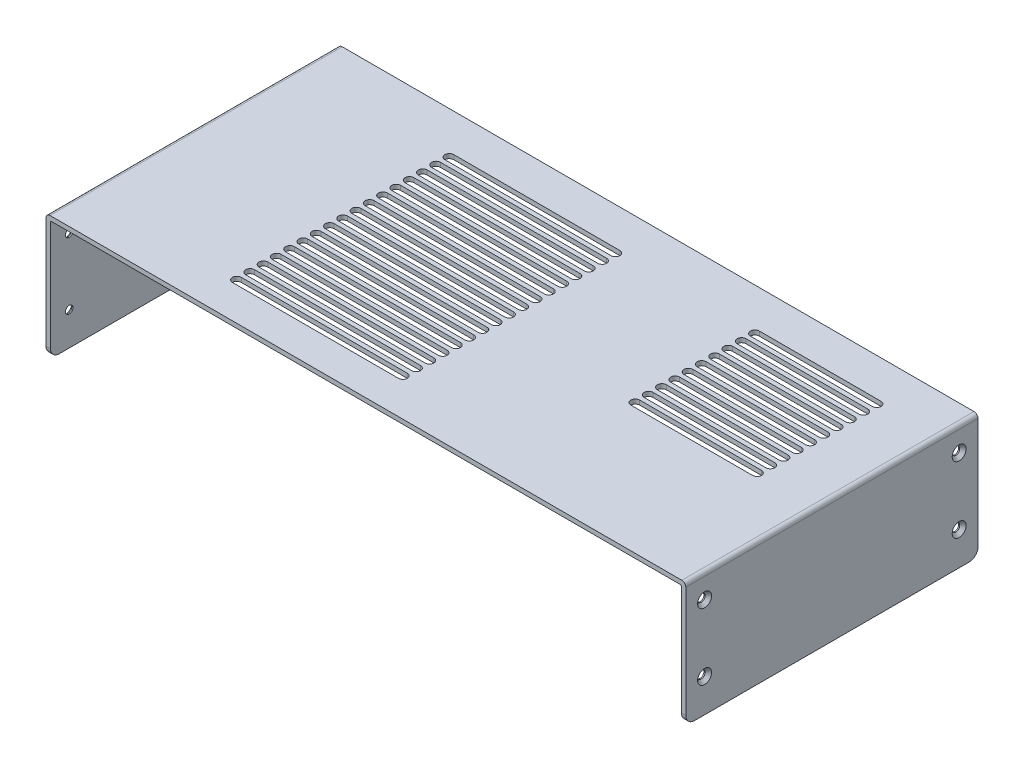
SolidWorks part; units mm, degrees
ref_plane "Front Plane" through (0, 0, 0) normal (0, 0, 1) x (1, 0, 0)
ref_plane "Top Plane" through (0, 0, 0) normal (0, 1, 0) x (1, 0, 0)
ref_plane "Right Plane" through (0, 0, 0) normal (1, 0, 0) x (0, 0, -1)
sketch "Sketch1" plane through (0, 0, 0) normal (0, 0, 1) x (1, 0, 0)
  line L0 (0, 0) -> (-2, 0)
  line L1 (-2, 0) -> (-2, 54.2)
  line L2 (-0.2, 56) -> (285.2, 56)
  line L3 (287, 54.2) -> (287, 0)
  line L4 (287, 0) -> (285, 0)
  line L5 (285, 0) -> (285, 53.5)
  line L6 (284.5, 54) -> (0.5, 54)
  line L7 (0, 53.5) -> (0, 0)
  arc A0 (285, 53.5) -> (284.5, 54) centre (284.5, 53.5) ccw
  arc A1 (0.5, 54) -> (0, 53.5) centre (0.5, 53.5) ccw
  arc A2 (-2, 54.2) -> (-0.2, 56) centre (-0.2, 54.2) cw
  arc A3 (285.2, 56) -> (287, 54.2) centre (285.2, 54.2) cw
  point P13 (0, 54)
  dimension "D5" = 0.5
  dimension "D6" = 1.8
  dimension "D1" = 54
  dimension "D2" = 285
  dimension "D3" = 2
  dimension "D4" = 2
extrude "Boss-Extrude1" add sketch "Sketch1" along normal blind 132
hole_wizard "CSK for M3 Flat Head Machine Screw1" positions "Sketch3" profile "Sketch2" countersink size "M3" standard "Ansi Metric"
sketch "Sketch3" plane through (-2, 0, 0) normal (-1, 0, 0) x (0, 0, 1)
  point P0 (8.5, 45)
  point P1 (8.5, 15)
  point P3 (123.5, 45)
  point P5 (123.5, 15)
sketch "Sketch2" plane through (-2, 45, 8.5) normal (0, 1, 0) x (0, 0, 1)
  line L0 (0, 0) -> (0, 6.0215)
  line L1 (0, 6.0215) -> (1.7, 5)
  line L2 (1.7, 5) -> (1.7, 1.45)
  line L3 (1.7, 1.45) -> (3.15, 0)
  line L5 (3.15, 0) -> (0, 0)
  line L6 (-1.7, 1.45) -> (-3.15, 0) construction
  line L10 (0, 6.0215) -> (-1.7, 5) construction
  line L11 (0, -6.35) -> (0, 107.95) construction
  dimension "Hole Dia." = 3.4
  dimension "Hole Depth" = 5
  dimension "Near C'Sink Dia." = 6.3
  dimension "Near C'Sink Angle" = 90
  dimension "Drill Angle" = 118
hole_wizard "CSK for M3 Flat Head Machine Screw2" positions "Sketch5" profile "Sketch4" countersink size "M3" standard "Ansi Metric"
sketch "Sketch5" plane through (287, 0, 0) normal (1, 0, 0) x (0, 0, -1)
  point P0 (-123.5, 45)
  point P1 (-123.5, 15)
  point P3 (-8.5, 45)
  point P5 (-8.5, 15)
sketch "Sketch4" plane through (287, 45, 123.5) normal (0, 1, 0) x (0, 0, -1)
  line L0 (0, 0) -> (0, 6.0215)
  line L1 (0, 6.0215) -> (1.7, 5)
  line L2 (1.7, 5) -> (1.7, 1.45)
  line L3 (1.7, 1.45) -> (3.15, 0)
  line L5 (3.15, 0) -> (0, 0)
  line L6 (-1.7, 1.45) -> (-3.15, 0) construction
  line L10 (0, 6.0215) -> (-1.7, 5) construction
  line L11 (0, -6.35) -> (0, 107.95) construction
  dimension "Hole Dia." = 3.4
  dimension "Hole Depth" = 5
  dimension "Near C'Sink Dia." = 6.3
  dimension "Near C'Sink Angle" = 90
  dimension "Drill Angle" = 118
sketch "Sketch6" plane through (0, 56, 0) normal (0, 1, 0) x (1, 0, 0)
  line L0 (67.2, -19) -> (142.2, -19) construction
  line L1 (67.2, -17) -> (142.2, -17)
  line L2 (67.2, -21) -> (142.2, -21)
  line L3 (285.2, 0) -> (-0.2, 0) construction
  line L6 (285.2, -132) -> (285.2, 0) construction
  arc A0 (67.2, -17) -> (67.2, -21) centre (67.2, -19) ccw
  arc A1 (142.2, -21) -> (142.2, -17) centre (142.2, -19) ccw
  point P2 (104.7, -19)
  dimension "D3" = 2
  dimension "D1" = 19
  dimension "D2" = 143
  dimension "D4" = 75
extrude "Cut-Extrude1" cut sketch "Sketch6" against normal blind 5
pattern_linear "LPattern1" count 17 spacing 6 along (0, 0, 1) of "Cut-Extrude1"
sketch "Sketch7" plane through (0, 56, 0) normal (0, 1, 0) x (1, 0, 0)
  line L0 (205.2, -19) -> (260.2, -19) construction
  line L1 (205.2, -17) -> (260.2, -17)
  line L2 (205.2, -21) -> (260.2, -21)
  line L3 (285.2, -132) -> (285.2, 0) construction
  line L4 (285.2, 0) -> (-0.2, 0) construction
  arc A0 (205.2, -17) -> (205.2, -21) centre (205.2, -19) ccw
  arc A1 (260.2, -21) -> (260.2, -17) centre (260.2, -19) ccw
  point P2 (232.7, -19)
  dimension "D3" = 2
  dimension "D1" = 25
  dimension "D2" = 80
  dimension "D4" = 19
extrude "Cut-Extrude2" cut sketch "Sketch7" against normal blind 200
pattern_linear "LPattern2" count 10 spacing 6 along (0, 0, 1) of "Cut-Extrude2"
fillet "Fillet1" radius 4 4 edges at (286, 0, 132) (286, 0, 0) (-1, 0, 132) (-1, 0, 0)
